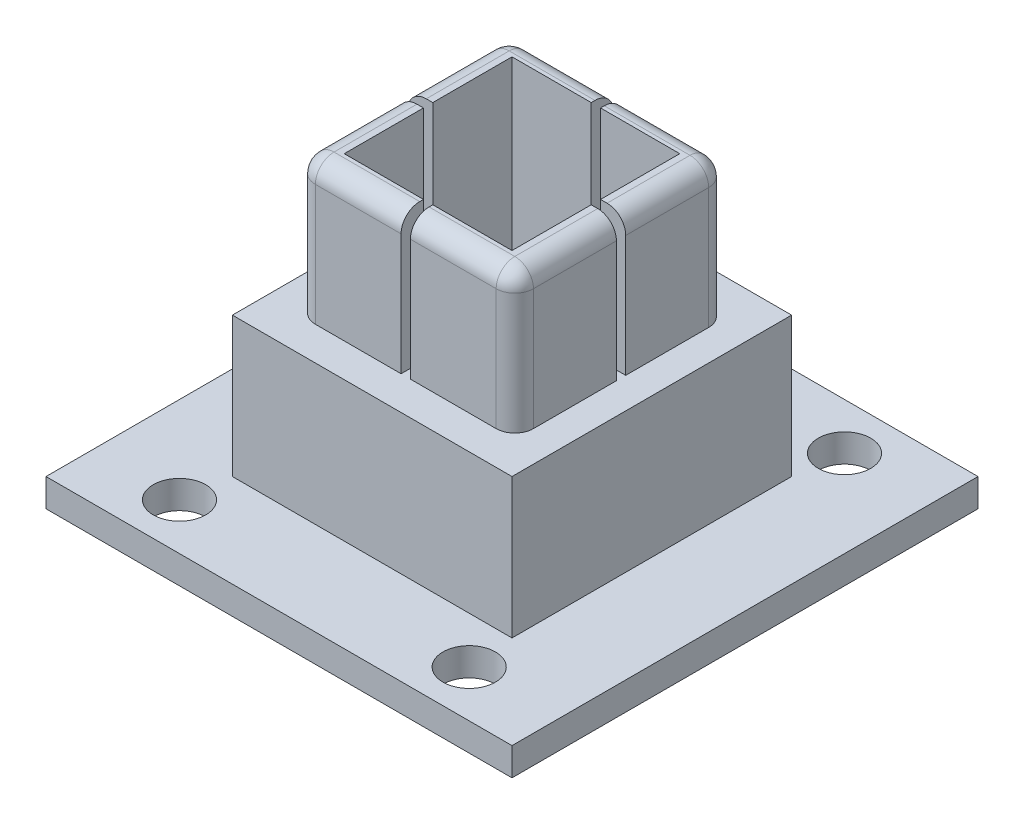
SolidWorks part; units mm, degrees
ref_plane "Alzado" through (0, 0, 0) normal (0, 0, 1) x (1, 0, 0)
ref_plane "Planta" through (0, 0, 0) normal (0, 1, 0) x (1, 0, 0)
ref_plane "Vista lateral" through (0, 0, 0) normal (1, 0, 0) x (0, 0, -1)
sketch "Croquis1" plane through (0, 0, 0) normal (0, 1, 0) x (1, 0, 0)
  line L1 (-25, 25) -> (25, 25)
  line L2 (-25, 25) -> (-25, -25)
  line L3 (-25, -25) -> (25, -25)
  line L4 (25, 25) -> (25, -25)
  line L5 (-25, 25) -> (25, -25) construction
  line L6 (-25, -25) -> (25, 25) construction
  point P0 (0, 0)
  dimension "D1" = 50
  dimension "D2" = 50
extrude "Saliente-Extruir1" add sketch "Croquis1" along normal blind 3
sketch "Croquis2" plane through (0, 3, 0) normal (0, 1, 0) x (1, 0, 0)
  line L1 (-15, 15) -> (15, 15)
  line L2 (-15, 15) -> (-15, -15)
  line L3 (-15, -15) -> (15, -15)
  line L4 (15, 15) -> (15, -15)
  line L5 (-15, 15) -> (15, -15) construction
  line L6 (-15, -15) -> (15, 15) construction
  line L7 (-9, 9) -> (9, 9)
  line L8 (-9, 9) -> (-9, -9)
  line L9 (-9, -9) -> (9, -9)
  line L10 (9, 9) -> (9, -9)
  line L11 (-9, 9) -> (9, -9) construction
  line L12 (-9, -9) -> (9, 9) construction
  point P0 (0, 0)
  point P6 (0, 0)
  dimension "D1" = 30
  dimension "D2" = 30
  dimension "D3" = 6
extrude "Saliente-Extruir2" add sketch "Croquis2" along normal blind 30
sketch "Croquis3" plane through (0, 3, 0) normal (0, 1, 0) x (1, 0, 0)
  line L0 (25, -20) -> (-25, -20) construction
  line L1 (25, -25) -> (25, 25) construction
  line L2 (-25, 25) -> (-25, -25) construction
  line L3 (25, 20) -> (-25, 20) construction
  line L4 (0, -25) -> (0, -15) construction
  line L5 (-25, -25) -> (25, -25) construction
  line L6 (-15, -15) -> (15, -15) construction
  line L7 (0, 15) -> (0, 25) construction
  line L8 (15, 15) -> (-15, 15) construction
  line L9 (25, 25) -> (-25, 25) construction
  line L10 (15.6762, -25) -> (15.6762, 25) construction
  line L11 (-15.6762, -25) -> (-15.6762, 25) construction
  circle A0 centre (15.4054, -20) radius 2.8139
  circle A1 centre (-15.6762, -20) radius 2.8139
  circle A2 centre (15.6762, 20) radius 2.8139
  circle A3 centre (-15.6762, 20) radius 2.8139
  point P22 (0, -20)
  point P29 (0, 20)
extrude "Cortar-Extruir1" cut sketch "Croquis3" against normal blind 10
sketch "Croquis4" plane through (0, 33, 0) normal (0, 1, 0) x (1, 0, 0)
  line L1 (15, -15) -> (-15, -15)
  line L2 (15, -15) -> (15, 15)
  line L3 (15, 15) -> (-15, 15)
  line L4 (-15, -15) -> (-15, 15)
  line L5 (11.7, -11.4) -> (-11.7, -11.4)
  line L6 (11.7, -11.4) -> (11.7, 11.4)
  line L7 (11.7, 11.4) -> (-11.7, 11.4)
  line L8 (-11.7, -11.4) -> (-11.7, 11.4)
  line L9 (11.7, -11.4) -> (-11.7, 11.4) construction
  line L10 (11.7, 11.4) -> (-11.7, -11.4) construction
  point P6 (0, 0)
  dimension "D1" = 3.3
  dimension "D2" = 3.6
extrude "Cortar-Extruir2" cut sketch "Croquis4" against normal blind 15
fillet "Redondeo1" radius 2 8 edges at (0, 33, 11.4) (-11.7, 25.5, 11.4) (-11.7, 33, 0) (-11.7, 25.5, -11.4) (0, 33, -11.4) (11.7, 33, 0) (11.7, 25.5, -11.4) (11.7, 25.5, 11.4)
sketch "Croquis5" plane through (0, 0, 0) normal (0, -1, 0) x (1, 0, 0)
  line L0 (-9, -9) -> (-9, 9) construction
  line L1 (-9, 9) -> (9, 9)
  line L2 (-9, 9) -> (-9, -9)
  line L3 (-9, -9) -> (9, -9)
  line L4 (9, 9) -> (9, -9)
  line L5 (-9, 9) -> (9, -9) construction
  line L6 (-9, -9) -> (9, 9) construction
  line L7 (-9, 9) -> (9, 9) construction
  point P0 (0, 0)
extrude "Cortar-Extruir3" cut sketch "Croquis5" against normal offset from surface (16 mm away) 2 up to face at (0, 18, 0)
sketch "Croquis6" plane through (-11.7, 0, 0) normal (-1, 0, 0) x (0, 0, 1)
  line L0 (0, 33.2941) -> (0, 18) construction
  line L1 (-9.4, 18) -> (9.4, 18) construction
  line L3 (-0.5, 33.2941) -> (0.5, 33.2941)
  line L4 (-0.5, 33.2941) -> (-0.5, 18)
  line L5 (-0.5, 18) -> (0.5, 18)
  line L6 (0.5, 33.2941) -> (0.5, 18)
  dimension "D1" = 1
extrude "Cortar-Extruir4" cut sketch "Croquis6" against normal through all
sketch "Croquis7" plane through (0, 0, 11.4) normal (0, 0, 1) x (1, 0, 0)
  line L0 (0, 33.2345) -> (0, 18) construction
  line L1 (-9.7, 18) -> (9.7, 18) construction
  line L3 (-0.5, 33.2345) -> (0.5, 33.2345)
  line L4 (-0.5, 33.2345) -> (-0.5, 18)
  line L5 (-0.5, 18) -> (0.5, 18)
  line L6 (0.5, 33.2345) -> (0.5, 18)
  dimension "D1" = 1
extrude "Cortar-Extruir5" cut sketch "Croquis7" against normal through all
